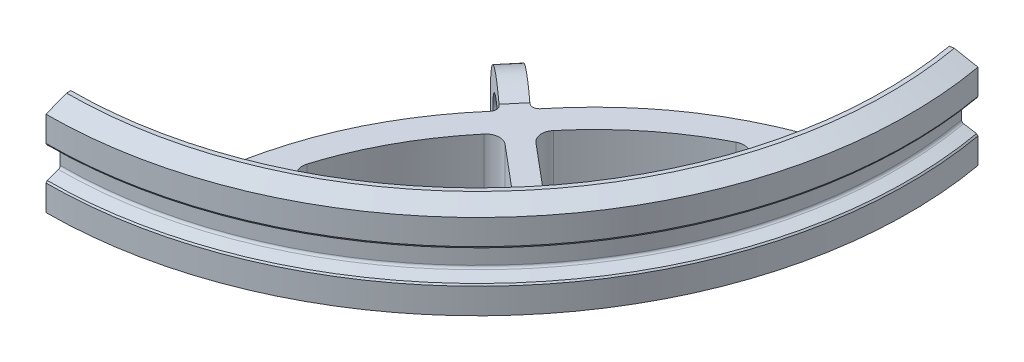
SolidWorks part; units mm, degrees
ref_plane "Front Plane" through (0, 0, 0) normal (0, 0, 1) x (1, 0, 0)
ref_plane "Top Plane" through (0, 0, 0) normal (0, 1, 0) x (1, 0, 0)
ref_plane "Right Plane" through (0, 0, 0) normal (1, 0, 0) x (0, 0, -1)
sketch "Sketch1" plane through (0, 0, 0) normal (1, 0, 0) x (0, 0, -1)
  line L0 (8.255, 9.8559) -> (8.001, 9.6019)
  line L1 (8.001, 9.6019) -> (3.3175, 9.6019)
  line L3 (3, 9.2844) -> (3, 3.3242)
  line L5 (3.2089, 3.0259) -> (5.4418, 2.2132)
  line L6 (5.4418, 2.2132) -> (5.6275, 1.8916)
  line L7 (5.6275, 1.8916) -> (5.6275, 0.254)
  line L8 (5.6275, 0.254) -> (5.3735, 0)
  line L9 (5.3735, 0) -> (0, 0)
  line L11 (0, 12.0097) -> (6.1625, 12.0097)
  line L12 (6.1625, 12.0097) -> (8.255, 10.1908)
  line L13 (8.255, 10.1908) -> (8.255, 9.8559)
  line L38 (0, 12.0097) -> (0, 0)
  line L39 (0, 6.0049) -> (83.82, 6.0049) construction
  line L40 (83.82, 6.0049) -> (83.82, 9.8559) construction
  arc A2 (3, 9.2844) -> (3.3175, 9.6019) centre (3.3175, 9.2844) cw
  arc A3 (3.2089, 3.0259) -> (3, 3.3242) centre (3.3175, 3.3242) cw
  dimension "D1" = 0.3175
  dimension "D2" = 3
  dimension "D3" = 3.2089
  dimension "D4" = 5.3735
  dimension "D5" = 5.4418
  dimension "D6" = 5.6275
  dimension "D7" = 6.1625
  dimension "D8" = 8.001
  dimension "D9" = 8.255
  dimension "D10" = 83.82
  dimension "D11" = 0.254
  dimension "D12" = 1.8916
  dimension "D13" = 2.2132
  dimension "D14" = 6.0049
  dimension "D15" = 9.6019
  dimension "D19" = 10.1908
sketch "Sketch2" plane through (0, 0, 0) normal (1, 0, 0) x (0, 0, -1)
  line L0 (8.3044, 9.4019) -> (7.5034, 9.4019)
  line L1 (7.5034, 9.4019) -> (3.7034, 7.9019)
  line L2 (3.7034, 7.9019) -> (3.7034, 3.2103)
  line L3 (3.7034, 3.2103) -> (3.889, 2.8888)
  line L4 (3.889, 2.8888) -> (5.9966, 2.1217)
  line L5 (6.3309, 1.6443) -> (6.3309, -1.6443)
  line L6 (5.9966, -2.1217) -> (3.942, -2.8695)
  line L7 (3.942, -2.8695) -> (3.7034, -3.1539)
  line L8 (3.7034, -3.1539) -> (3.7034, -7.9019)
  line L9 (3.7034, -7.9019) -> (7.5034, -9.4019)
  line L10 (7.5034, -9.4019) -> (8.3044, -9.4019)
  line L11 (8.3044, -9.4019) -> (8.3044, 9.4019)
  arc A0 (6.3309, 1.6443) -> (5.9966, 2.1217) centre (5.8229, 1.6443) ccw
  arc A1 (5.9966, -2.1217) -> (6.3309, -1.6443) centre (5.8229, -1.6443) ccw
  dimension "D1" = 0.508
  dimension "D2" = 3.7034
  dimension "D3" = 3.889
  dimension "D4" = 3.942
  dimension "D5" = 5.8229
  dimension "D6" = 5.9966
  dimension "D7" = 1.6443
  dimension "D8" = 7.5034
  dimension "D9" = 8.3044
  dimension "D10" = 3.2103
  dimension "D11" = 7.9019
  dimension "D12" = 9.4019
  dimension "D13" = 1.6443
  dimension "D14" = 7.9019
ref_axis "Axis1" through (0, 6.0049, -83.82) along (0, 1, 0)
revolve "Revolve5" add sketch "Sketch2" angle 100 about axis through (0, 6.0049, -83.82) along (0, 1, 0)
sketch "Sketch3" plane through (0, 0, 0) normal (0, 1, 0) x (1, 0, 0)
  line L0 (0, 83.82) -> (61.3729, 32.322) construction
  line L1 (-8.509, 92.329) -> (8.509, 92.329) construction
  line L2 (-8.509, 92.329) -> (-8.509, 75.311) construction
  line L3 (-8.509, 75.311) -> (8.509, 75.311) construction
  line L4 (8.509, 92.329) -> (8.509, 75.311) construction
  line L5 (-8.509, 92.329) -> (8.509, 75.311) construction
  line L6 (-8.509, 75.311) -> (8.509, 92.329) construction
  line L7 (78.8995, 97.7321) -> (0, 83.82) construction
  circle A0 centre (0, 83.82) radius 6.35 construction
  circle A1 centre (0, 83.82) radius 12.0335 construction
  arc A2 (0, 3.7034) -> (78.8995, 97.7321) centre (0, 83.82) ccw construction
  point P0 (0, 83.82)
  dimension "D1" = 17.018
  dimension "D2" = 17.018
sketch "Sketch4" plane through (0, 0, 0) normal (0, 1, 0) x (1, 0, 0)
  line L0 (37.4174, 49.9006) -> (41.3089, 46.6352)
  line L3 (57.1692, 33.3268) -> (59.7815, 36.44)
  line L5 (30.6734, 53.9373) -> (30.6876, 53.9254)
  line L6 (2.0409, 86.2522) -> (63.4138, 34.7542)
  line L7 (34.7551, 58.8017) -> (34.7693, 58.7898)
  line L15 (31.5795, 54.7979) -> (34.1918, 57.9111) construction
  line L18 (37.4174, 49.9006) -> (40.0297, 53.0138)
  line L19 (41.3089, 46.6352) -> (43.9212, 49.7484) construction
  line L21 (57.1692, 33.3268) -> (45.2092, 43.3625)
  line L23 (38.7236, 51.4572) -> (42.6151, 48.1918) construction
  line L26 (59.7815, 36.44) -> (47.8214, 46.4757)
  line L27 (40.0297, 53.0138) -> (43.9212, 49.7484)
  line L29 (24.7733, 11.2214) -> (30.2969, 13.514)
  line L30 (75.5402, 72.0559) -> (74.2555, 66.2031)
  arc A0 (0, 7.5034) -> (75.1572, 97.0722) centre (0, 83.82) ccw construction
  spline S0 degree 3 poles (41.3089, 46.6352) (32.1707, 36.4097) (26.6584, 24.6046) (24.7733, 11.2214) knots 0 0 0 0 0.95123 0.95123 0.95123 0.95123
  spline S1 degree 3 poles (43.9212, 49.7484) (52.3196, 60.4156) (62.8597, 67.8518) (75.5402, 72.0559) knots 0 0 0 0 0.941704 0.941704 0.941704 0.941704
  spline S2 degree 3 poles (47.8214, 46.4757) (47.8442, 46.5083) (47.867, 46.5408) (47.8898, 46.5734) (47.8936, 46.5788) (47.9013, 46.5897) (47.9127, 46.6061) (47.921, 46.6166) (47.9251, 46.6218) (47.9265, 46.6236) (47.9293, 46.6271) (47.9334, 46.6324) (47.9362, 46.6359) (47.9376, 46.6377) (48.427, 47.2586) (49.4401, 48.4996) (51.5223, 50.874) (54.2536, 53.6666) (57.7124, 56.712) (61.3587, 59.46) (65.1957, 61.9145) (69.2339, 64.0805) (72.2958, 65.4375) (74.0038, 66.1063) (74.2555, 66.2031) knots 0 0 0 0 0.003266 0.003266 0.003266 0.003813 0.004361 0.004908 0.004908 0.004908 0.005093 0.005277 0.005462 0.005462 0.005462 0.070457 0.136559 0.268764 0.400969 0.533174 0.665379 0.797583 0.929788 0.952526 0.952526 0.952526 0.952526
  spline S3 degree 3 poles (45.2092, 43.3625) (45.1811, 43.3345) (45.153, 43.3064) (45.1249, 43.2783) (45.1202, 43.2736) (45.1108, 43.2641) (45.0966, 43.25) (45.0878, 43.2401) (45.0833, 43.2351) (45.0818, 43.2334) (45.0788, 43.2301) (45.0743, 43.2251) (45.0714, 43.2217) (45.0699, 43.22) (44.5434, 42.6302) (43.4971, 41.417) (41.5203, 38.9541) (39.2444, 35.7795) (36.846, 31.8444) (34.7728, 27.7762) (33.022, 23.5713) (31.5901, 19.2183) (30.7541, 15.8408) (30.3715, 13.9096) (30.2969, 13.514) knots 0 0 0 0 0.003266 0.003266 0.003266 0.003813 0.004361 0.004908 0.004908 0.004908 0.005093 0.005277 0.005462 0.005462 0.005462 0.070457 0.136559 0.268764 0.400969 0.533174 0.665379 0.797583 0.929788 0.963696 0.963696 0.963696 0.963696
  dimension "D1" = 5.08
  dimension "D3" = 3.175
extrude "Boss-Extrude1" add sketch "Sketch4" along normal blind 7.62 and the other way blind 6.35 contours L21 S3 L29 S0 L0 L18 L27 S1 L30 S2 L26 L3
sketch "Sketch6" plane through (40.0312, 0, -47.7073) normal (-0.6428, 0, 0.766) x (0.766, 0, 0.6428)
  circle A0 centre (-4.3746, 0.564) radius 4.699
  circle A1 centre (-4.3746, 0.564) radius 8.382
  dimension "D1" = 9.398
extrude "Boss-Extrude2" add sketch "Sketch6" against normal blind 4.064
sketch "Sketch7" plane through (40.0312, 0, -47.7073) normal (-0.6428, 0, 0.766) x (0.766, 0, 0.6428)
  circle A0 centre (-4.3746, 0.564) radius 4.699
  dimension "D1" = 9.398
extrude "Cut-Extrude1" cut sketch "Sketch7" against normal blind 4.064
fillet "Fillet6" radius 2.54 8 edges at (24.9737, 0.635, -12.5534) (30.5439, 0.635, -14.7571) (56.5873, 0.635, -33.8151) (45.2092, 0.635, -43.3625) (47.8214, 0.635, -46.4757) (59.1955, 0.635, -36.9318) (73.3452, 0.635, -65.8452) (74.5392, 0.635, -71.7157)
fillet "Fillet7" radius 1.27 2 edges at (41.3089, 0.635, -46.6352) (43.9212, 0.635, -49.7484)
